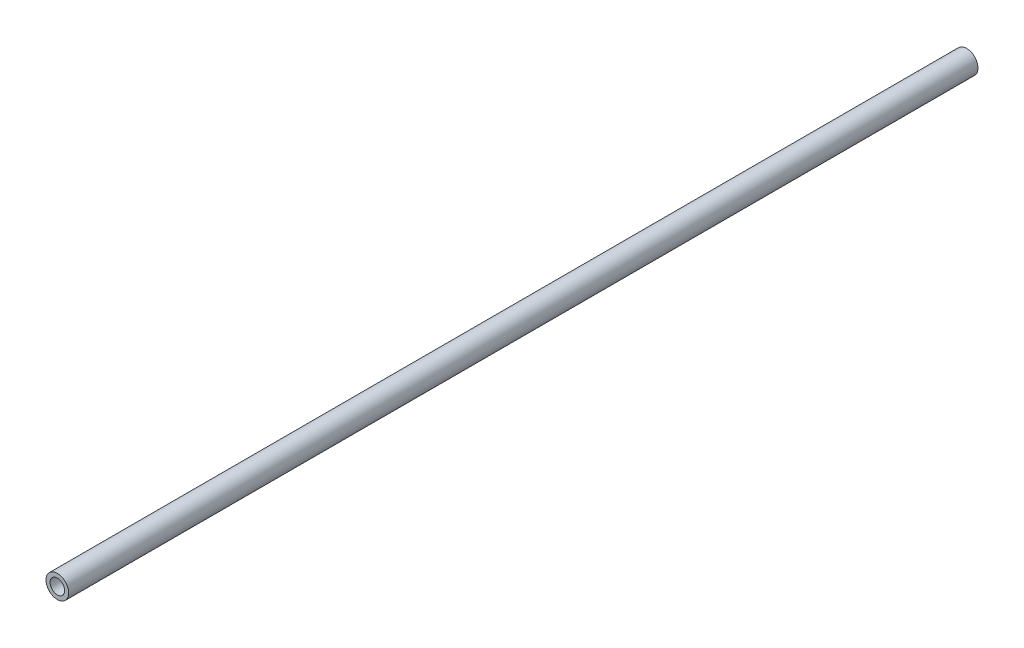
SolidWorks part; units mm, degrees
ref_plane "Front" through (0, 0, 0) normal (0, 0, 1) x (1, 0, 0)
ref_plane "Top" through (0, 0, 0) normal (0, 1, 0) x (1, 0, 0)
ref_plane "Right" through (0, 0, 0) normal (1, 0, 0) x (0, 0, -1)
sketch "Sketch1" plane through (0, 0, 0) normal (0, 0, 1) x (1, 0, 0)
  circle A0 centre (0, 0) radius 1.6
  circle A1 centre (0, 0) radius 2.5
extrude "Boss-Extrude2" add sketch "Sketch1" along normal blind 200
